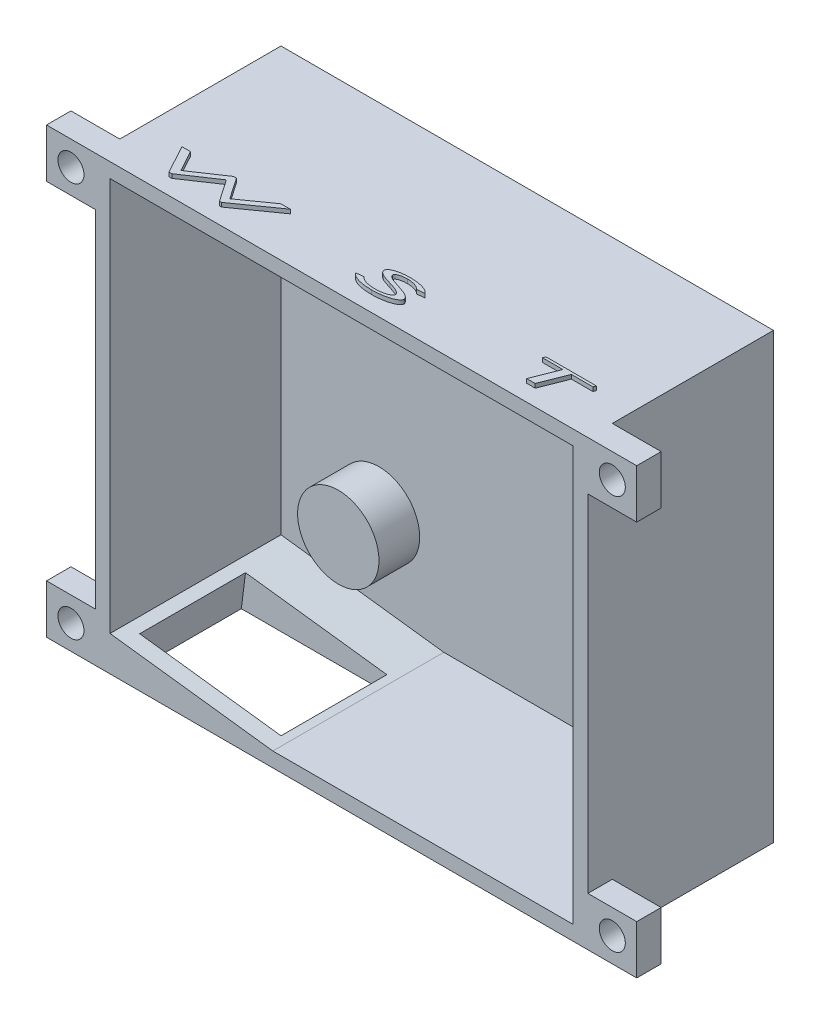
SolidWorks part; units mm, degrees
ref_plane "Alzado" through (0, 0, 0) normal (0, 0, 1) x (1, 0, 0)
ref_plane "Planta" through (0, 0, 0) normal (0, 1, 0) x (1, 0, 0)
ref_plane "Vista lateral" through (0, 0, 0) normal (1, 0, 0) x (0, 0, -1)
sketch "Croquis1" plane through (0, 0, 0) normal (0, 0, 1) x (1, 0, 0)
  line L1 (0, 0) -> (-60.5, 0)
  line L2 (0, 0) -> (0, 54.5)
  line L3 (0, 54.5) -> (-60.5, 54.5)
  line L4 (-60.5, 0) -> (-60.5, 54.5)
  dimension "D1" = 60.5
  dimension "D2" = 54.5
extrude "Saliente-Extruir1" add sketch "Croquis1" along normal blind 22.8
sketch "Croquis3" plane through (0, 0, 22.8) normal (0, 0, 1) x (1, 0, 0)
  line L8 (-1.8, 1.8) -> (-1.8, 52.7)
  line L9 (-1.8, 52.7) -> (-58.7, 52.7)
  line L10 (-58.7, 52.7) -> (-58.7, 1.8)
  line L11 (-58.7, 1.8) -> (-1.8, 1.8)
  line L12 (-1.8, 1.8) -> (-1.8, 52.7)
  line L13 (-1.8, 52.7) -> (-58.7, 52.7)
  line L14 (-58.7, 52.7) -> (-58.7, 1.8)
  line L15 (-58.7, 1.8) -> (-1.8, 1.8)
  dimension "D1" = 1.8
extrude "Cortar-Extruir1" cut sketch "Croquis3" against normal blind 21
sketch "Croquis5" plane through (0, 0, 1.8) normal (0, 0, 1) x (1, 0, 0)
  line L0 (-1.8, 52.7) -> (-58.7, 1.8) construction
  line L1 (-1.8, 1.8) -> (-1.8, 52.7) construction
  line L2 (-1.8, 52.7) -> (-58.7, 52.7) construction
  line L4 (-58.7, 1.8) -> (-1.8, 1.8) construction
  line L5 (-1.8, 52.7) -> (-58.7, 52.7) construction
  line L6 (-1.8, 1.8) -> (-12.3, 1.8)
  line L7 (-1.8, 1.8) -> (-1.8, 9.8)
  line L8 (-1.8, 9.8) -> (-12.3, 9.8)
  line L9 (-12.3, 1.8) -> (-12.3, 9.8)
  line L10 (-58.7, 52.7) -> (-58.7, 1.8) construction
  line L12 (-51.7, 52.7) -> (-43.7, 52.7)
  line L13 (-51.7, 52.7) -> (-51.7, 45.2)
  line L14 (-51.7, 45.2) -> (-43.7, 45.2)
  line L15 (-43.7, 52.7) -> (-43.7, 45.2)
  circle A1 centre (-26.3, 26.2) radius 24.5 construction
  circle A6 centre (-8.3, 5.8) radius 2.1
  circle A7 centre (-47.7, 49.2) radius 2.1
  circle A8 centre (-10.4959, 44.9211) radius 5
  circle A9 centre (-46.6593, 12.571) radius 5
  dimension "D1" = 6.5
  dimension "D2" = 49
  dimension "D7" = 4
  dimension "D9" = 4.2
  dimension "D11" = 11
  dimension "D12" = 4
  dimension "D5" = 4
  dimension "D6" = 4.2
  dimension "D3" = 24.5
  dimension "D4" = 26.5
  dimension "D8" = 4
  dimension "D10" = 3.5
  dimension "D13" = 4
  dimension "D14" = 4
extrude "Saliente-Extruir2" add sketch "Croquis5" along normal blind 5
sketch "Croquis9" plane through (0, 54.5, 0) normal (0, 1, 0) x (1, 0, 0)
  text T0 "W" font "Century Gothic" height 3.5
  text T1 "S" font "Century Gothic" height 3.5
  text T2 "T" font "Century Gothic" height 3.5
sketch "Croquis10" plane through (0, 0, 22.8) normal (0, 0, 1) x (1, 0, 0)
  line L0 (-30.25, 52.7) -> (-30.25, 1.8) construction
  line L1 (-60.5, 54.5) -> (-66.5, 54.5)
  line L2 (-60.5, 54.5) -> (-60.5, 48.5)
  line L3 (-60.5, 48.5) -> (-66.5, 48.5)
  line L4 (-66.5, 54.5) -> (-66.5, 48.5)
  line L5 (-1.8, 52.7) -> (-58.7, 52.7) construction
  line L6 (-58.7, 1.8) -> (-1.8, 1.8) construction
  line L7 (6, 54.5) -> (6, 48.5)
  line L8 (0, 48.5) -> (6, 48.5)
  line L9 (0, 54.5) -> (0, 48.5)
  line L10 (0, 54.5) -> (6, 54.5)
  line L11 (-58.7, 27.25) -> (-1.8, 27.25) construction
  line L12 (-58.7, 52.7) -> (-58.7, 1.8) construction
  line L13 (-1.8, 1.8) -> (-1.8, 52.7) construction
  line L14 (0, 0) -> (6, 0)
  line L15 (0, 0) -> (0, 6)
  line L16 (0, 6) -> (6, 6)
  line L17 (6, 0) -> (6, 6)
  line L18 (-66.5, 0) -> (-66.5, 6)
  line L19 (-60.5, 6) -> (-66.5, 6)
  line L20 (-60.5, 0) -> (-60.5, 6)
  line L21 (-60.5, 0) -> (-66.5, 0)
  circle A0 centre (-63.5, 51.5) radius 1.6
  circle A1 centre (3, 51.5) radius 1.6
  circle A2 centre (3, 3) radius 1.6
  circle A3 centre (-63.5, 3) radius 1.6
  dimension "D1" = 6
  dimension "D2" = 6
extrude "Saliente-Extruir3" add sketch "Croquis10" against normal blind 3
sketch "Croquis11" plane through (0, 0, 22.8) normal (0, 0, 1) x (1, 0, 0)
  line L0 (-58.7, 1.8) -> (-38.7, 1.8)
  line L1 (-58.7, 1.8) -> (-1.8, 1.8) construction
  line L2 (-38.7, 1.8) -> (-58.7, 4.3)
  line L3 (-58.7, 52.7) -> (-58.7, 1.8) construction
  line L4 (-58.7, 4.3) -> (-58.7, 1.8)
  dimension "D1" = 20
  dimension "D2" = 2.5
extrude "Saliente-Extruir4" add sketch "Croquis11" against normal up to surface (21 mm away) up to face at (-41.6593, 12.571, 1.8)
sketch "Croquis12" plane through (-0.3738, -2.9908, 0) normal (0.124, 0.9923, 0) x (0.9923, -0.124, 0)
  line L0 (-38.6244, -1.8) -> (-38.6244, -22.8) construction
  line L1 (-39.6244, -7.8) -> (-57.1244, -7.8)
  line L2 (-39.6244, -7.8) -> (-39.6244, -20.8)
  line L3 (-39.6244, -20.8) -> (-57.1244, -20.8)
  line L4 (-57.1244, -7.8) -> (-57.1244, -20.8)
  line L5 (-38.6244, -22.8) -> (-58.7801, -22.8) construction
  dimension "D1" = 1
  dimension "D2" = 2
  dimension "D3" = 13
  dimension "D4" = 17.5
extrude "Cortar-Extruir5" cut sketch "Croquis12" against normal up to surface (1.939 mm away)
extrude "Saliente-Extruir5" add sketch "Croquis9" along normal blind 0.5
